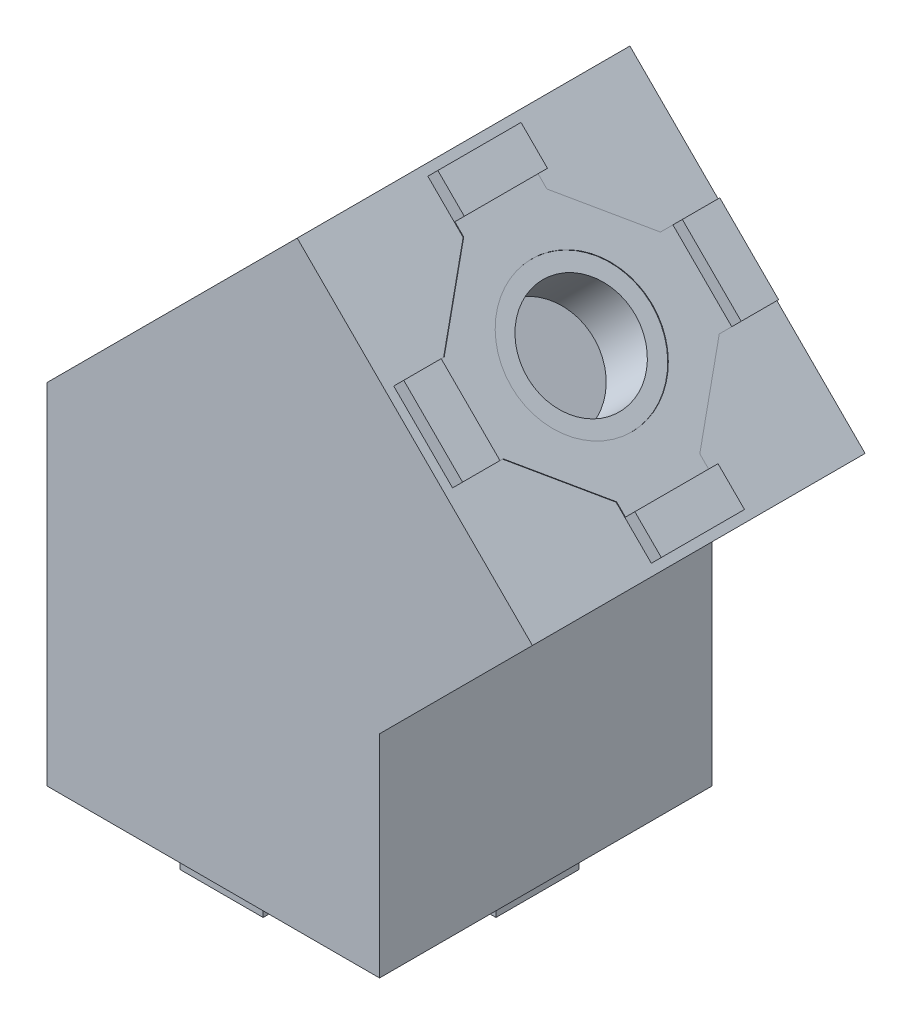
SolidWorks part; units mm, degrees
material "6063-T6"
ref_plane "Plane1" through (0, 0, 0) normal (0, 0, 1) x (1, 0, 0)
ref_plane "Plane2" through (0, 0, 0) normal (0, 1, 0) x (1, 0, 0)
ref_plane "Plane3" through (0, 0, 0) normal (1, 0, 0) x (0, 0, -1)
sketch "Эскиз2" plane through (0, 0, 0) normal (0, 1, 0) x (1, 0, 0)
  line L1 (-20, 20) -> (20, 20)
  line L2 (-20, 20) -> (-20, -20)
  line L3 (-20, -20) -> (20, -20)
  line L4 (20, 20) -> (20, -20)
  line L5 (-20, 20) -> (20, -20) construction
  line L6 (-20, -20) -> (20, 20) construction
  point P0 (0, 0)
  dimension "D1" = 40
  dimension "D2" = 40
extrude "Бобышка-Вытянуть1" add sketch "Эскиз2" along normal blind 42
sketch "Эскиз4" plane through (0, 0, 20) normal (0, 0, 1) x (1, 0, 0)
  line L0 (20, 42) -> (-20, 42)
  line L1 (-20, 42) -> (20, 25.4315)
  line L2 (20, 42) -> (20, 0) construction
  line L3 (20, 42) -> (20, 25.4315)
  dimension "D1" = 22.5
extrude "Вырез-Вытянуть1" cut sketch "Эскиз4" against normal blind 42
sketch "Эскиз5" plane through (0, 0, 0) normal (0, 1, 0) x (1, 0, 0)
  line L2 (-20, 15.4) -> (15.4, 15.4)
  line L6 (-20, 20) -> (20, 20) construction
  line L8 (-20, 15.4) -> (-20, -15.4)
  line L9 (-20, -15.4) -> (15.4, -15.4)
  line L11 (15.4, -15.4) -> (15.4, 15.4)
  line L13 (-20, -20) -> (20, -20) construction
  line L14 (20, 20) -> (20, -20) construction
  line L15 (-20, 20) -> (-20, -20) construction
  point P0 (0, 0)
  dimension "D1" = 4.6
  dimension "D2" = 4.6
  dimension "D3" = 4.6
extrude "Вырез-Вытянуть2" cut sketch "Эскиз5" along normal blind 42 from offset 7
sketch "Эскиз6" plane through (0, 0, 20) normal (0, 0, 1) x (1, 0, 0)
  line L0 (20, 25.4315) -> (38.3848, 43.8162)
  line L1 (20, 25.4315) -> (20, 0) construction
  line L2 (-20, 42) -> (10.1005, 72.1005)
  line L3 (10.1005, 72.1005) -> (38.3848, 43.8162)
  line L8 (20, 0) -> (20, 25.4315)
  line L9 (20, 25.4315) -> (-20, 42)
  line L10 (-20, 42) -> (-20, 0)
  line L11 (-20, 0) -> (20, 0)
  line L13 (20, 25.4315) -> (-20, 42)
  dimension "D1" = 135
  dimension "D2" = 26
  dimension "D3" = 0
extrude "Бобышка-Вытянуть2" add sketch "Эскиз6" against normal up to surface (40 mm away) contours L2 L3 L0 L13 up to face at (0, 16.8579, -20)
sketch "Эскиз7" plane through (41.1005, 41.1005, 0) normal (0.7071, 0.7071, 0) x (0, 0, -1)
  line L0 (-15.5, 43.8406) -> (-15.5, 8.3406)
  line L1 (20, 43.8406) -> (-20, 43.8406) construction
  line L2 (-15.5, 8.3406) -> (15.5, 8.3406)
  line L3 (15.5, 8.3406) -> (15.5, 43.8406)
  line L4 (15.5, 43.8406) -> (-15.5, 43.8406)
  line L5 (-20, 43.8406) -> (-20, 3.8406) construction
  line L6 (20, 3.8406) -> (-20, 3.8406) construction
  line L7 (20, 3.8406) -> (20, 43.8406) construction
  dimension "D1" = 4.5
  dimension "D2" = 4.5
  dimension "D3" = 4.5
extrude "Вырез-Вытянуть3" cut sketch "Эскиз7" against normal up to surface (20.864 mm away) from offset 7 offset against normal yes
sketch "Эскиз8" plane through (-20, 0, 0) normal (-1, 0, 0) x (0, 0, 1)
  line L0 (-16.4, 42) -> (-16.4, 4)
  line L1 (-20, 42) -> (-15.5, 42) construction
  line L2 (-16.4, 4) -> (16.4, 4)
  line L3 (16.4, 4) -> (16.4, 42)
  line L4 (15.5, 42) -> (20, 42) construction
  line L5 (16.4, 42) -> (15.4, 42)
  line L8 (15.4, 42) -> (15.4, 7)
  line L9 (15.4, 7) -> (-15.4, 7)
  line L10 (-15.4, 7) -> (-15.4, 42)
  line L11 (-15.4, 42) -> (-16.4, 42)
  point P5 (18.1044, 4.9971)
  point P10 (15.4, 42)
  point P20 (-49.7708, 30.0738)
  point P21 (0, 0)
  dimension "D1" = 1
  dimension "D2" = 1
  dimension "D3" = 3
extrude "Вырез-Вытянуть4" cut sketch "Эскиз8" against normal blind 1
sketch "Эскиз12" plane through (-31, 31, 0) normal (-0.7071, 0.7071, 0) x (0, 0, 1)
  line L0 (-16.4, 15.5563) -> (-16.4, 54.1249)
  line L1 (-16.4, 54.1249) -> (16.4, 54.1249)
  line L2 (16.4, 54.1249) -> (16.4, 15.5563)
  line L3 (16.4, 15.5563) -> (15.5, 15.5563)
  line L4 (15.5, 15.5563) -> (15.5, 51.1249)
  line L5 (15.5, 51.1249) -> (-15.5, 51.1249)
  line L9 (-16.4, 15.5563) -> (-15.5, 15.5563)
  line L10 (-15.5, 15.5563) -> (-15.5, 51.1249)
  dimension "D1" = 3
extrude "Вырез-Вытянуть5" cut sketch "Эскиз12" against normal blind 1
sketch "Эскиз14" plane through (-19, 0, 0) normal (-1, 0, 0) x (0, 0, 1)
  line L0 (-15.5, 41.5858) -> (-15.5, 7)
  line L1 (-15.5, 7) -> (15.5, 7)
  line L2 (15.5, 7) -> (15.5, 41.5858)
  line L3 (15.5, 41.5858) -> (-15.5, 41.5858)
  line L4 (15.4, 7) -> (-15.4, 7) construction
extrude "Вырез-Вытянуть7" cut sketch "Эскиз14" against normal up to vertex (34.5 mm away)
sketch "Эскиз15" plane through (41.1005, 41.1005, 0) normal (0.7071, 0.7071, 0) x (0, 0, -1)
  line L0 (-20, 43.8406) -> (20, 3.8406) construction
  line L1 (20, 43.8406) -> (-20, 3.8406) construction
  circle A0 centre (0, 23.8406) radius 6.5
  dimension "D1" = 13
extrude "Вырез-Вытянуть8" cut sketch "Эскиз15" against normal blind 10
sketch "Эскиз16" plane through (0, 0, 0) normal (0, -1, 0) x (1, 0, 0)
  line L0 (-20, 20) -> (20, -20) construction
  line L1 (20, 20) -> (-20, -20) construction
  circle A0 centre (0, 0) radius 6.5
  dimension "D1" = 13
extrude "Вырез-Вытянуть9" cut sketch "Эскиз16" against normal blind 10 contours A0
sketch "Эскиз17" plane through (41.1005, 41.1005, 0) normal (0.7071, 0.7071, 0) x (0, 0, -1)
  line L16 (0, 43.8406) -> (0, 23.8406) construction
  line L17 (20, 43.8406) -> (-20, 43.8406) construction
  line L18 (0, 23.8406) -> (-20, 23.8406) construction
  line L19 (-20, 43.8406) -> (-20, 3.8406) construction
  line L20 (0, 23.8406) -> (20, 23.8406) construction
  line L21 (20, 3.8406) -> (20, 43.8406) construction
  line L22 (0, 42.8406) -> (-5, 42.8406)
  line L23 (-5, 42.8406) -> (-5, 36.8406)
  line L24 (-19, 23.8406) -> (-19, 28.8406)
  line L25 (-19, 28.8406) -> (-13, 28.8406)
  line L26 (-13, 28.8406) -> (-5, 36.8406)
  line L27 (-19, 23.8406) -> (-19, 18.8406)
  line L28 (-19, 18.8406) -> (-13, 18.8406)
  line L29 (-13, 18.8406) -> (-5, 10.8406)
  line L30 (-5, 10.8406) -> (-5, 4.8406)
  line L31 (-5, 4.8406) -> (5, 4.8406)
  line L32 (5, 4.8406) -> (5, 10.8406)
  line L33 (5, 10.8406) -> (13, 18.8406)
  line L34 (13, 18.8406) -> (19, 18.8406)
  line L35 (19, 18.8406) -> (19, 28.8406)
  line L36 (19, 28.8406) -> (13, 28.8406)
  line L37 (13, 28.8406) -> (5, 36.8406)
  line L38 (5, 36.8406) -> (5, 42.8406)
  line L39 (5, 42.8406) -> (0, 42.8406)
  line L40 (20, 3.8406) -> (-20, 3.8406) construction
  circle A0 centre (0, 23.8406) radius 8.5
  point P30 (19, 23.8406)
  dimension "D10" = 17
  dimension "D1" = 1
  dimension "D2" = 5
  dimension "D3" = 1
  dimension "D4" = 6
  dimension "D5" = 5
  dimension "D6" = 6
  dimension "D7" = 1
  dimension "D8" = 1
  dimension "D9" = 6
extrude "Вырез-Вытянуть10" cut sketch "Эскиз17" against normal blind 3.5
sketch "Эскиз19" plane through (38.6256, 38.6256, 0) normal (0.7071, 0.7071, 0) x (0, 0, -1)
  line L0 (-19, 28.8406) -> (-19, 18.8406) construction
  line L1 (-14, 37.8406) -> (14, 37.8406)
  line L2 (-14, 37.8406) -> (-14, 9.8406)
  line L3 (-14, 9.8406) -> (14, 9.8406)
  line L4 (14, 37.8406) -> (14, 9.8406)
  line L5 (-14, 37.8406) -> (14, 9.8406) construction
  line L6 (-14, 9.8406) -> (14, 37.8406) construction
  line L7 (5, 42.8406) -> (-5, 42.8406) construction
  circle A1 centre (0, 23.8406) radius 6.5
  circle A2 centre (0, 23.8406) radius 6.5 construction
  point P0 (0, 23.8406)
  dimension "D1" = 5
  dimension "D2" = 5
extrude "Бобышка-Вытянуть3" add sketch "Эскиз19" along normal offset from surface (2 mm away) 1.5 up to face at (24.2426, 57.9584, 0)
sketch "Эскиз20" plane through (0, 0, 0) normal (0, -1, 0) x (1, 0, 0)
  line L0 (0, 20) -> (0, 0) construction
  line L1 (0, 0) -> (-20, 0) construction
  line L2 (0, 0) -> (20, 0) construction
  line L3 (0, 19) -> (-5, 19)
  line L4 (-5, 19) -> (-5, 13)
  line L5 (-19, 0) -> (-19, 5)
  line L6 (-19, 5) -> (-13, 5)
  line L7 (-13, 5) -> (-5, 13)
  line L8 (-19, 0) -> (-19, -5)
  line L9 (-19, -5) -> (-13, -5)
  line L10 (-13, -5) -> (-5, -13)
  line L11 (-5, -13) -> (-5, -19)
  line L12 (-5, -19) -> (5, -19)
  line L13 (5, -19) -> (5, -13)
  line L14 (5, -13) -> (13, -5)
  line L15 (13, -5) -> (19, -5)
  line L16 (19, -5) -> (19, 5)
  line L17 (19, 5) -> (13, 5)
  line L18 (13, 5) -> (5, 13)
  line L19 (5, 13) -> (5, 19)
  line L20 (5, 19) -> (0, 19)
  line L21 (-20, -20) -> (-20, 20) construction
  line L22 (20, -20) -> (20, 20) construction
  line L23 (-20, 20) -> (20, 20) construction
  line L24 (20, -20) -> (-20, -20) construction
  circle A0 centre (0, 0) radius 8.5
  circle A1 centre (0, 0) radius 6.5 construction
  point P22 (19, 0)
  point P24 (0, 0)
  point P25 (0, 0)
  point P26 (0, 0)
  point P29 (0, 0)
  point P32 (0, 0)
  point P37 (0, 0)
  dimension "D6" = 17
  dimension "D1" = 5
  dimension "D2" = 6
  dimension "D3" = 5
  dimension "D4" = 6
  dimension "D5" = 6
  dimension "D7" = 1
  dimension "D8" = 1
  dimension "D9" = 1
  dimension "D10" = 1
extrude "Вырез-Вытянуть11" cut sketch "Эскиз20" against normal blind 3.5
sketch "Эскиз21" plane through (0, 3.5, 0) normal (0, -1, 0) x (1, 0, 0)
  line L0 (-19, 5) -> (-19, -5) construction
  line L1 (-14, 14) -> (14, 14)
  line L2 (-14, 14) -> (-14, -14)
  line L3 (-14, -14) -> (14, -14)
  line L4 (14, 14) -> (14, -14)
  line L5 (-14, 14) -> (14, -14) construction
  line L6 (-14, -14) -> (14, 14) construction
  line L7 (5, 19) -> (-5, 19) construction
  circle A0 centre (0, 0) radius 6.5
  circle A1 centre (0, 0) radius 6.5 construction
  point P0 (0, 0)
  dimension "D1" = 5
  dimension "D2" = 5
extrude "Бобышка-Вытянуть4" add sketch "Эскиз21" along normal offset from surface (2 mm away) 1.5 up to face at (0, 0, 0)
sketch "Эскиз22" plane through (0, 0, 16.4) normal (0, 0, -1) x (-1, 0, 0)
  line L0 (-7.9085, 68.4943) -> (-7.2014, 69.2014)
  line L1 (-7.2014, 69.2014) -> (20, 42)
  line L2 (20, 42) -> (20, 4.1)
  line L3 (20, 4.1) -> (19, 4.1)
  line L4 (19, 4.1) -> (19, 41.5858)
  line L5 (19, 41.5858) -> (-7.9085, 68.4943)
  line L6 (-7.9792, 68.565) -> (-7.2721, 69.2721) construction
  line L7 (19, 4) -> (20, 4) construction
  point P4 (0, 0)
  point P13 (0, 0)
  point P14 (0, 0)
  point P17 (0, 0)
  point P18 (0, 0)
  dimension "D1" = 0.1
  dimension "D2" = 0.1
extrude "Бобышка-Вытянуть5" add sketch "Эскиз22" along direction (0, 0, -1) on the side of the normal offset from surface (32.6 mm away) 0.1 from offset 0.1
sketch "Эскиз23" plane through (40.0398, 40.0398, 0) normal (0.7071, 0.7071, 0) x (0, 0, -1)
  line L0 (-19, 18.8406) -> (-19, 28.8406)
  line L1 (-19, 28.8406) -> (-13, 28.8406)
  line L2 (-13, 28.8406) -> (-5, 36.8406)
  line L3 (-5, 36.8406) -> (-5, 42.8406)
  line L4 (-5, 42.8406) -> (5, 42.8406)
  line L5 (5, 42.8406) -> (5, 36.8406)
  line L6 (5, 36.8406) -> (13, 28.8406)
  line L7 (13, 28.8406) -> (19, 28.8406)
  line L8 (19, 28.8406) -> (19, 18.8406)
  line L9 (19, 18.8406) -> (13, 18.8406)
  line L10 (13, 18.8406) -> (5, 10.8406)
  line L11 (5, 10.8406) -> (5, 4.8406)
  line L12 (5, 4.8406) -> (-5, 4.8406)
  line L13 (-5, 4.8406) -> (-5, 10.8406)
  line L14 (-5, 10.8406) -> (-13, 18.8406)
  line L15 (-13, 18.8406) -> (-19, 18.8406)
  circle A0 centre (0, 23.8406) radius 8.5
  circle A1 centre (0, 23.8406) radius 8.5 construction
extrude "Бобышка-Вытянуть6" add sketch "Эскиз23" along normal blind 1.6
sketch "Эскиз24" plane through (41.1712, 41.1712, 0) normal (0.7071, 0.7071, 0) x (0, 0, -1)
  line L0 (5, 36.8406) -> (5, 42.8406) construction
  line L1 (-5, 42.8406) -> (5, 42.8406)
  line L2 (-5, 42.8406) -> (-5, 38.3406)
  line L3 (-5, 38.3406) -> (5, 38.3406)
  line L4 (5, 42.8406) -> (5, 38.3406)
  line L5 (-13, 28.8406) -> (-19, 28.8406) construction
  line L6 (-19, 18.8406) -> (-14.5, 18.8406)
  line L7 (-19, 18.8406) -> (-19, 28.8406)
  line L8 (-19, 28.8406) -> (-14.5, 28.8406)
  line L9 (-14.5, 18.8406) -> (-14.5, 28.8406)
  line L10 (5, 4.8406) -> (5, 10.8406) construction
  line L11 (-5, 4.8406) -> (5, 4.8406)
  line L12 (-5, 4.8406) -> (-5, 9.3406)
  line L13 (-5, 9.3406) -> (5, 9.3406)
  line L14 (5, 4.8406) -> (5, 9.3406)
  line L15 (19, 28.8406) -> (13, 28.8406) construction
  line L16 (19, 18.8406) -> (14.5, 18.8406)
  line L17 (19, 18.8406) -> (19, 28.8406)
  line L18 (19, 28.8406) -> (14.5, 28.8406)
  line L19 (14.5, 18.8406) -> (14.5, 28.8406)
  point P28 (0, 4.8406)
  dimension "D1" = 4.5
  dimension "D2" = 4.5
  dimension "D3" = 4.5
  dimension "D4" = 4.5
extrude "Бобышка-Вытянуть7" add sketch "Эскиз24" along normal blind 1.6
sketch "Эскиз25" plane through (0, 1.5, 0) normal (0, -1, 0) x (1, 0, 0)
  line L0 (-5, 13) -> (-5, 19)
  line L1 (-5, 19) -> (5, 19)
  line L2 (5, 19) -> (5, 13)
  line L3 (5, 13) -> (13, 5)
  line L4 (13, 5) -> (19, 5)
  line L5 (19, 5) -> (19, -5)
  line L6 (19, -5) -> (13, -5)
  line L7 (13, -5) -> (5, -13)
  line L8 (5, -13) -> (5, -19)
  line L9 (5, -19) -> (-5, -19)
  line L10 (-5, -19) -> (-5, -13)
  line L11 (-5, -13) -> (-13, -5)
  line L12 (-13, -5) -> (-19, -5)
  line L13 (-19, -5) -> (-19, 5)
  line L14 (-19, 5) -> (-13, 5)
  line L15 (-13, 5) -> (-5, 13)
  circle A0 centre (0, 0) radius 8.5
  circle A1 centre (0, 0) radius 8.5 construction
extrude "Бобышка-Вытянуть8" add sketch "Эскиз25" along normal blind 1.6
sketch "Эскиз26" plane through (0, -0.1, 0) normal (0, -1, 0) x (1, 0, 0)
  line L0 (5, 13) -> (5, 19) construction
  line L1 (-5, 19) -> (5, 19)
  line L2 (-5, 19) -> (-5, 14.5)
  line L3 (-5, 14.5) -> (5, 14.5)
  line L4 (5, 19) -> (5, 14.5)
  line L5 (13, -5) -> (19, -5) construction
  line L6 (19, 5) -> (14.5, 5)
  line L7 (19, 5) -> (19, -5)
  line L8 (19, -5) -> (14.5, -5)
  line L9 (14.5, 5) -> (14.5, -5)
  line L10 (5, -19) -> (5, -13) construction
  line L11 (-5, -19) -> (5, -19)
  line L12 (-5, -19) -> (-5, -14.5)
  line L13 (-5, -14.5) -> (5, -14.5)
  line L14 (5, -19) -> (5, -14.5)
  line L15 (-13, 5) -> (-19, 5) construction
  line L16 (-19, -5) -> (-14.5, -5)
  line L17 (-19, -5) -> (-19, 5)
  line L18 (-19, 5) -> (-14.5, 5)
  line L19 (-14.5, -5) -> (-14.5, 5)
  dimension "D1" = 4.5
  dimension "D2" = 4.5
  dimension "D3" = 4.5
  dimension "D4" = 4.5
extrude "Бобышка-Вытянуть9" add sketch "Эскиз26" along normal blind 1.6
